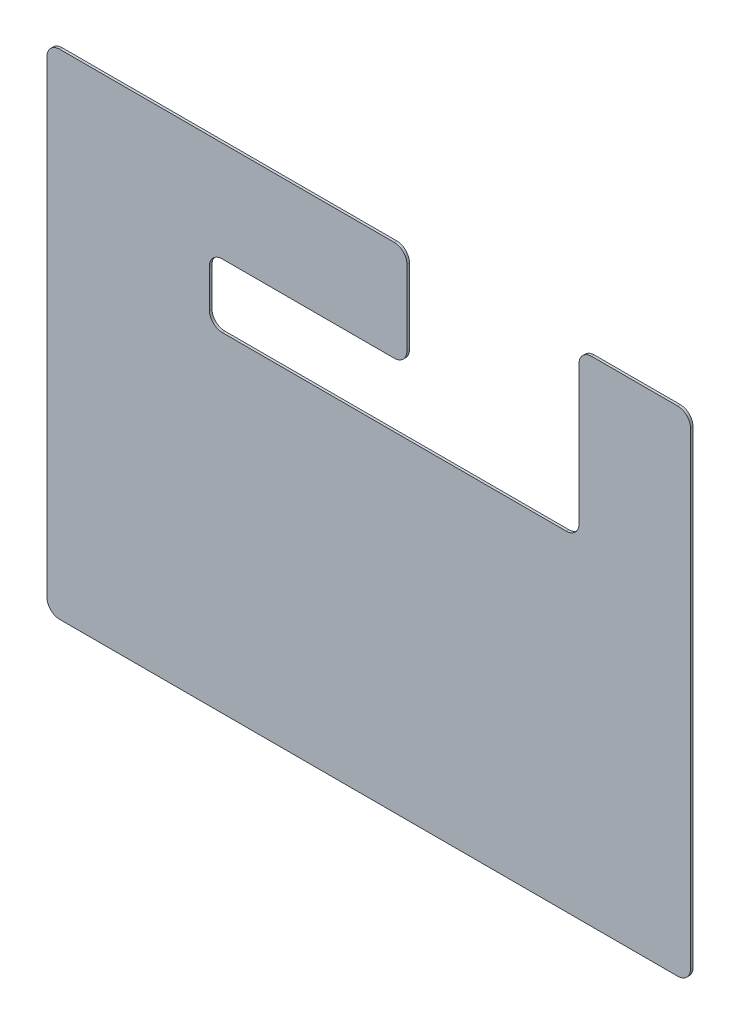
SolidWorks part; units mm, degrees
material "Acrylic (Medium-high impact)"
ref_plane "Front Plane" through (0, 0, 0) normal (0, 0, 1) x (1, 0, 0)
ref_plane "Top Plane" through (0, 0, 0) normal (0, 1, 0) x (1, 0, 0)
ref_plane "Right Plane" through (0, 0, 0) normal (1, 0, 0) x (0, 0, -1)
sketch "Sketch1" plane through (0, 0, 0) normal (0, 0, 1) x (1, 0, 0)
  line L1 (-500, -382.5) -> (500, -382.5) construction
  line L2 (-500, -382.5) -> (-500, 382.5) construction
  line L3 (-500, 382.5) -> (500, 382.5) construction
  line L4 (500, -382.5) -> (500, 382.5) construction
  line L5 (-500, -382.5) -> (500, 382.5) construction
  line L6 (-500, 382.5) -> (500, -382.5) construction
  line L7 (-505, -387.5) -> (505, -387.5)
  line L8 (-505, -387.5) -> (-505, 387.5)
  line L9 (-505, 387.5) -> (505, 387.5)
  line L10 (505, -387.5) -> (505, 387.5)
  line L11 (-505, -387.5) -> (505, 387.5) construction
  line L12 (-505, 387.5) -> (505, -387.5) construction
  point P0 (0, 0)
  dimension "D1" = 1000
  dimension "D2" = 765
  dimension "D3" = 5
  dimension "D4" = 5
extrude "Boss-Extrude1" add sketch "Sketch1" along normal blind 4
fillet "Fillet1" radius 20 4 edges at (-505, -387.5, 2) (-505, 387.5, 2) (505, 387.5, 2) (505, -387.5, 2)
sketch "Sketch2" plane through (0, 0, 4) normal (0, 0, 1) x (1, 0, 0)
  line L0 (0, 0) -> (0, 230) construction
  line L1 (250, 130) -> (-250, 130)
  line L2 (250, 130) -> (250, 230)
  line L3 (250, 230) -> (-250, 230)
  line L4 (-250, 130) -> (-250, 230)
  line L5 (195, 400) -> (195, 230) construction
  line L6 (330, 400) -> (60, 400)
  line L7 (330, 400) -> (330, 230)
  line L8 (330, 230) -> (60, 230)
  line L9 (60, 400) -> (60, 230)
  line L11 (250, 130) -> (330, 130)
  line L12 (250, 130) -> (250, 230)
  line L13 (250, 230) -> (330, 230)
  line L14 (330, 130) -> (330, 230)
  line M12 (485, 387.5) -> (-485, 387.5)
  dimension "D1" = 500
  dimension "D2" = 100
  dimension "D3" = 230
  dimension "D4" = 270
  dimension "D5" = 195
  dimension "D6" = 170
extrude "Cut-Extrude1" cut sketch "Sketch2" against normal blind 10 contours L9 L3 L8 L7 M12 | L4 L1 L2 L3 | L11 L14 L8 L2
fillet "Fillet2" radius 20 6 edges at (-250, 130, 2) (-250, 230, 2) (60, 387.5, 2) (330, 387.5, 2) (330, 130, 2) (60, 230, 2)
